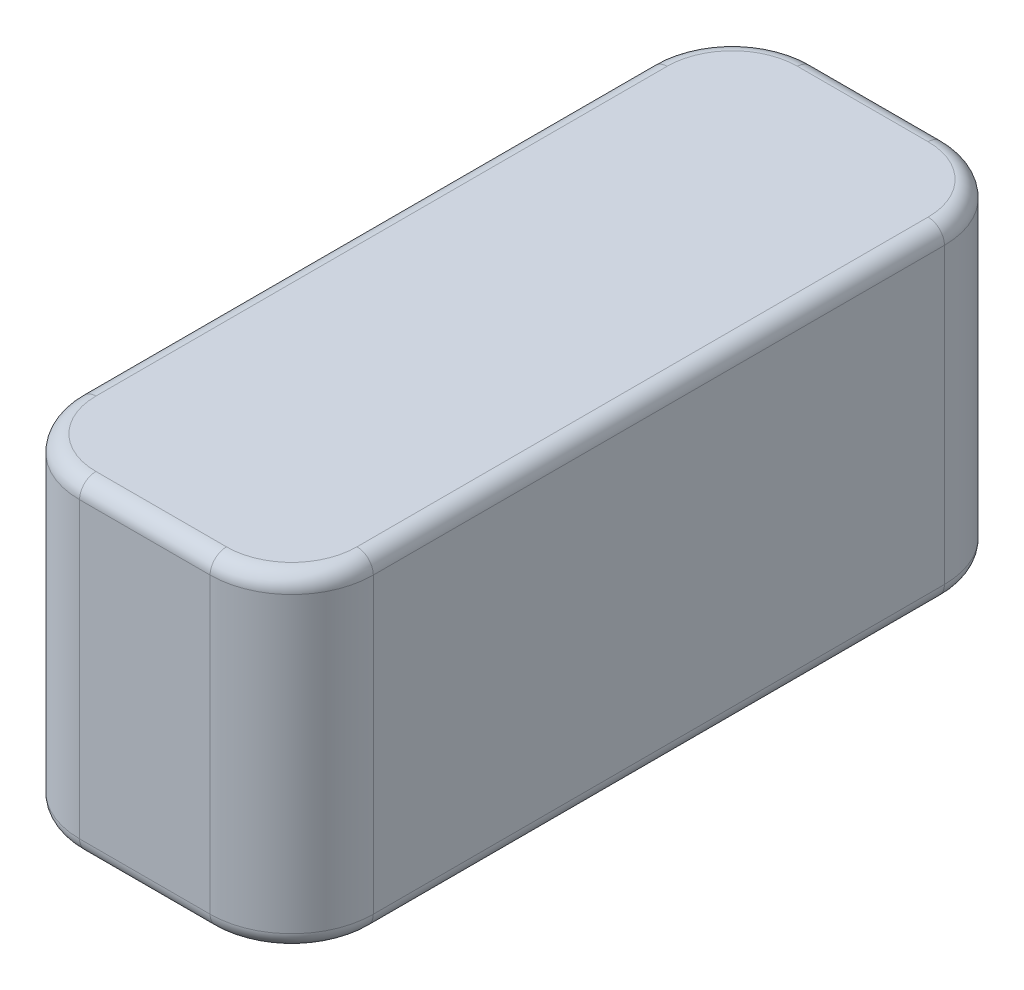
SolidWorks part; units mm, degrees
ref_plane "Front Plane" through (0, 0, 0) normal (0, 0, 1) x (1, 0, 0)
ref_plane "Top Plane" through (0, 0, 0) normal (0, 1, 0) x (1, 0, 0)
ref_plane "Right Plane" through (0, 0, 0) normal (1, 0, 0) x (0, 0, -1)
sketch "Sketch1" plane through (0, 0, 0) normal (0, 1, 0) x (1, 0, 0)
  line L1 (9, -22.5) -> (-9, -22.5)
  line L2 (9, -22.5) -> (9, 22.5)
  line L3 (9, 22.5) -> (-9, 22.5)
  line L4 (-9, -22.5) -> (-9, 22.5)
  line L5 (9, -22.5) -> (-9, 22.5) construction
  line L6 (9, 22.5) -> (-9, -22.5) construction
  point P0 (0, 0)
  dimension "D1" = 18
  dimension "D2" = 45
extrude "Boss-Extrude1" add sketch "Sketch1" along normal blind 20
fillet "Fillet1" radius 5 4 edges at (9, 10, 22.5) (-9, 10, 22.5) (9, 10, -22.5) (-9, 10, -22.5)
fillet "Fillet2" radius 1 16 edges at (7.5355, 0, -21.0355) (0, 0, -22.5) (-7.5355, 0, -21.0355) (-9, 0, 0) (-7.5355, 0, 21.0355) (0, 0, 22.5) (7.5355, 0, 21.0355) (9, 0, 0) (-7.5355, 20, 21.0355) (-9, 20, 0) (-7.5355, 20, -21.0355) (0, 20, -22.5) (7.5355, 20, -21.0355) (9, 20, 0) (7.5355, 20, 21.0355) (0, 20, 22.5)
ref_plane "Plane1" through (0, 19, 0) normal (0, 1, 0) x (1, 0, 0)
